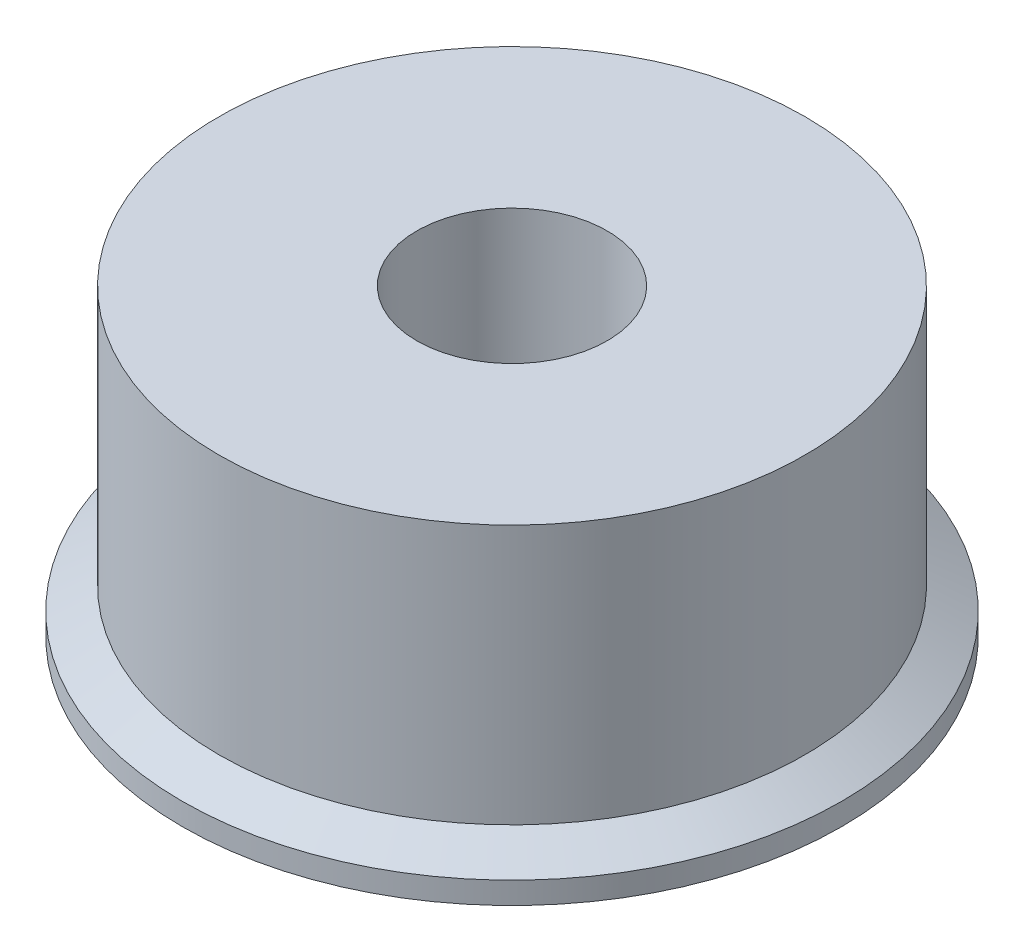
SolidWorks part; units mm, degrees
material "ABS"
ref_plane "Front Plane" through (0, 0, 0) normal (0, 0, 1) x (1, 0, 0)
ref_plane "Top Plane" through (0, 0, 0) normal (0, 1, 0) x (1, 0, 0)
ref_plane "Right Plane" through (0, 0, 0) normal (1, 0, 0) x (0, 0, -1)
sketch "Sketch1" plane through (0, 0, 0) normal (0, 0, 1) x (1, 0, 0)
  line L0 (0, 7.62) -> (0, 0) construction
  line L1 (0, -55) -> (0, 55) construction
  line L2 (-3.302, 10.524) -> (-10.16, 10.524)
  line L3 (-10.16, 10.524) -> (-10.16, 1.524)
  line L4 (-10.16, 1.524) -> (-11.43, 0.762)
  line L5 (-11.43, 0.762) -> (-11.43, 0)
  line L6 (55, 0) -> (-55, 0) construction
  line L7 (-11.43, 0) -> (-7.9375, 0)
  line L8 (-7.9375, 0) -> (-7.9375, 5.08)
  line L9 (-7.9375, 5.08) -> (-3.302, 5.08)
  line L11 (-3.302, 10.524) -> (-3.302, 5.08)
  dimension "D1" = 9
  dimension "D2" = 10.16
  dimension "D3" = 5.08
  dimension "D4" = 3.302
  dimension "D5" = 7.9375
  dimension "D6" = 0.762
  dimension "D7" = 1.27
  dimension "D8" = 1.524
revolve "Revolve1" add sketch "Sketch1" angle 360 about L0
